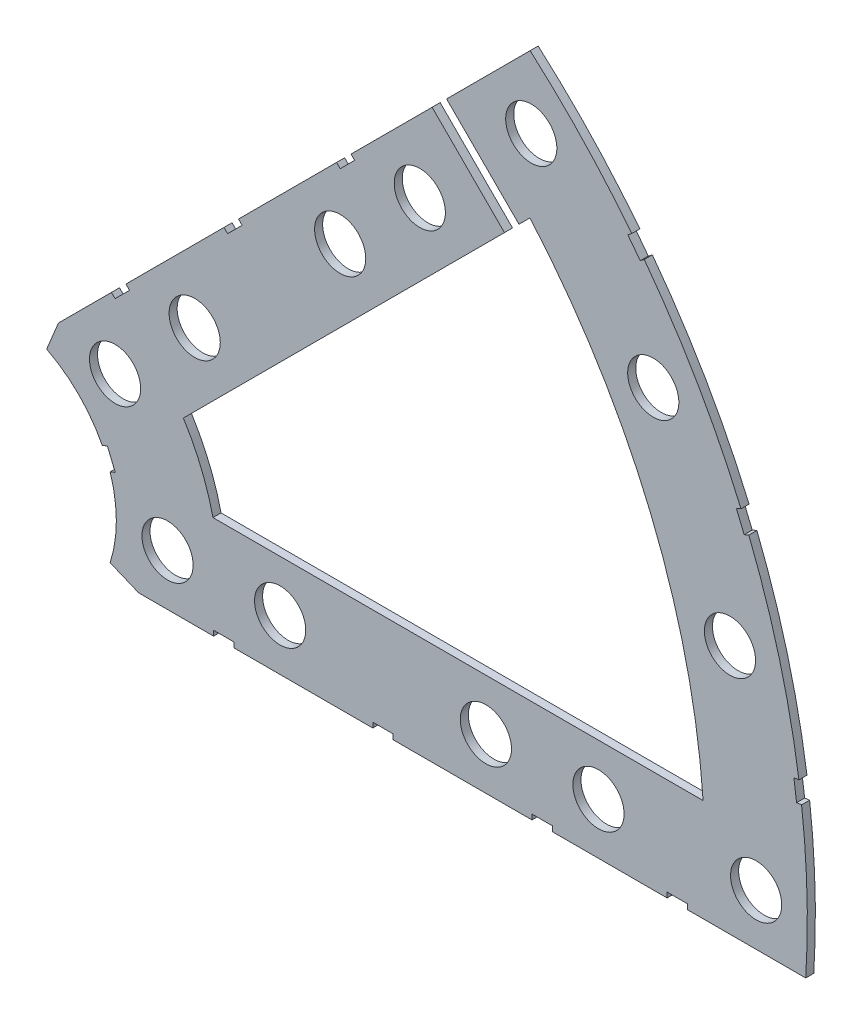
SolidWorks part; units mm, degrees
material "Copper"
ref_plane "Front Plane" through (0, 0, 0) normal (0, 0, 1) x (1, 0, 0)
ref_plane "Top Plane" through (0, 0, 0) normal (0, 1, 0) x (1, 0, 0)
ref_plane "Right Plane" through (0, 0, 0) normal (1, 0, 0) x (0, 0, -1)
sketch "Sketch1" plane through (0, 0, 0) normal (0, 0, 1) x (1, 0, 0)
  line L0 (0, 0) -> (320.3893, 0) construction
  line L1 (0, 0) -> (155.5285, 155.5285) construction
  line L2 (67.2115, 76.1917) -> (8.6967, 17.6769)
  line L3 (8.6967, 17.6769) -> (7.229, 14.1336)
  line L4 (101.4014, -6.35) -> (18.6489, -6.35)
  line L5 (15.1056, -4.8823) -> (18.6489, -6.35)
  line L6 (88.6729, 6.35) -> (27.8605, 6.35)
  line L9 (67.1914, 58.2111) -> (24.1905, 15.2102)
  line L10 (0, 0) -> (40.4486, 97.6516) construction
  line L11 (0, 0) -> (123.4567, -51.1374) construction
  line L18 (8.6967, 17.6769) -> (13.294, 8.6183) construction
  line L19 (18.6489, -6.35) -> (15.4943, 3.3063) construction
  line L20 (27.8605, 6.35) -> (27.7442, 6.7059) construction
  line L21 (24.1905, 15.2102) -> (24.3599, 14.8764) construction
  arc A0 (7.229, 14.1336) -> (15.1056, -4.8823) centre (0, 0) cw
  arc A1 (67.2115, 76.1917) -> (101.4014, -6.35) centre (0, 0) cw
  arc A2 (24.1905, 15.2102) -> (27.8605, 6.35) centre (0, 0) cw
  arc A3 (67.1914, 58.2111) -> (88.6729, 6.35) centre (0, 0) cw
  arc A8 (13.294, 8.6183) -> (15.4943, 3.3063) centre (0, 0) cw construction
  arc A9 (24.3599, 14.8764) -> (27.7442, 6.7059) centre (0, 0) cw construction
  dimension "D1" = 45
  dimension "D3" = 6.35
  dimension "D4" = 15.875
  dimension "D7" = 22.5
  dimension "D8" = 101.6
  dimension "D11" = 12.7
  dimension "D12" = 12.7
  dimension "D2" = 6.35
  dimension "D5" = 67.5
  dimension "D9" = 1.27
  dimension "D10" = 1.27
  dimension "D6" = 12.7
extrude "Boss-Extrude1" add sketch "Sketch1" along normal blind 1
sketch "Sketch2" plane through (0, 0, 1) normal (0, 0, 1) x (1, 0, 0)
  line L0 (0, 0) -> (101.6, 0) construction
  line L1 (0, 0) -> (71.842, 71.842) construction
  line L3 (0, 0) -> (22.225, 0) construction
  line L4 (0, 0) -> (15.7154, 15.7154) construction
  line L5 (0, 0) -> (95.25, 0) construction
  line L6 (0, 0) -> (92.0044, 24.6525) construction
  arc A0 (101.4014, -6.35) -> (67.2115, 76.1917) centre (0, 0) ccw construction
  circle A1 centre (22.225, 0) radius 3.175
  arc A2 (15.1056, -4.8823) -> (7.229, 14.1336) centre (0, 0) ccw construction
  circle A3 centre (36.195, 0) radius 3.175
  circle A4 centre (61.722, 0) radius 3.175
  circle A5 centre (75.692, 0) radius 3.175
  circle A6 centre (95.25, 0) radius 3.175
  circle A7 centre (15.7154, 15.7154) radius 3.175
  circle A8 centre (25.5937, 25.5937) radius 3.175
  circle A9 centre (43.644, 43.644) radius 3.175
  circle A10 centre (53.5223, 53.5223) radius 3.175
  circle A11 centre (92.0044, 24.6525) radius 3.175
  circle A12 centre (82.4889, 47.625) radius 3.175
  circle A13 centre (67.3519, 67.3519) radius 3.175
  dimension "D3" = 6.35
  dimension "D1" = 45
  dimension "D2" = 6.35
  dimension "D4" = 6.35
  dimension "D5" = 13.97
  dimension "D7" = 13.97
  dimension "D8" = 19.558
  dimension "D9" = 45
  dimension "D10" = 15
  dimension "D11" = 25.527
  dimension "D6" = 2
extrude "Cut-Extrude1" cut sketch "Sketch2" against normal through all
sketch "Sketch3" plane through (0, 0, 1) normal (0, 0, 1) x (1, 0, 0)
  line L0 (15.2664, 24.2467) -> (17.0625, 26.0427)
  line L1 (15.2664, 24.2467) -> (15.7154, 23.7977)
  line L2 (17.0625, 26.0427) -> (17.5115, 25.5937)
  line L3 (15.7154, 23.7977) -> (17.5115, 25.5937)
  line L4 (67.2115, 76.1917) -> (8.6967, 17.6769) construction
  line L5 (44.9911, 53.9713) -> (43.195, 52.1753)
  line L6 (44.9911, 53.9713) -> (45.4401, 53.5223)
  line L7 (43.195, 52.1753) -> (43.644, 51.7263)
  line L8 (45.4401, 53.5223) -> (43.644, 51.7263)
  line L9 (27.94, -6.35) -> (30.48, -6.35)
  line L10 (27.94, -6.35) -> (27.94, -5.715)
  line L11 (30.48, -6.35) -> (30.48, -5.715)
  line L12 (27.94, -5.715) -> (30.48, -5.715)
  line L13 (18.6489, -6.35) -> (101.4014, -6.35) construction
  line L14 (67.437, -6.35) -> (69.977, -6.35)
  line L15 (67.437, -6.35) -> (67.437, -5.715)
  line L16 (69.977, -6.35) -> (69.977, -5.715)
  line L17 (67.437, -5.715) -> (69.977, -5.715)
  line L18 (29.2307, 38.211) -> (31.0268, 40.007)
  line L19 (29.2307, 38.211) -> (29.6797, 37.762)
  line L20 (31.0268, 40.007) -> (31.4758, 39.558)
  line L21 (29.6797, 37.762) -> (31.4758, 39.558)
  line L22 (55.049, 64.0292) -> (56.845, 65.8253)
  line L23 (55.049, 64.0292) -> (64.0292, 55.049)
  line L24 (56.845, 65.8253) -> (65.8253, 56.845)
  line L25 (64.0292, 55.049) -> (65.8253, 56.845)
  line L26 (47.6885, -6.35) -> (50.2285, -6.35)
  line L27 (47.6885, -6.35) -> (47.6885, -5.715)
  line L28 (50.2285, -6.35) -> (50.2285, -5.715)
  line L29 (47.6885, -5.715) -> (50.2285, -5.715)
  line L30 (84.201, -6.35) -> (86.741, -6.35)
  line L31 (84.201, -6.35) -> (84.201, -5.715)
  line L32 (86.741, -6.35) -> (86.741, -5.715)
  line L33 (84.201, -5.715) -> (86.741, -5.715)
  line L34 (0, 0) -> (100.7308, 13.2615) construction
  line L35 (0, 0) -> (93.8662, 38.8806) construction
  line L36 (0, 0) -> (80.6047, 61.8502) construction
  line L37 (0, 0) -> (101.6, 0) construction
  line L38 (99.9355, 14.4377) -> (100.267, 11.9194)
  line L39 (99.9355, 14.4377) -> (101.1946, 14.6035)
  line L40 (100.267, 11.9194) -> (101.5261, 12.0852)
  line L41 (101.1946, 14.6035) -> (101.5261, 12.0852)
  line L42 (99.9355, 14.4377) -> (101.5261, 12.0852) construction
  line L43 (100.267, 11.9194) -> (101.1946, 14.6035) construction
  line L44 (93.7655, 37.4643) -> (94.9388, 37.9503)
  line L45 (93.7655, 37.4643) -> (92.7935, 39.811)
  line L46 (94.9388, 37.9503) -> (93.9668, 40.297)
  line L47 (92.7935, 39.811) -> (93.9668, 40.297)
  line L48 (93.7655, 37.4643) -> (93.9668, 40.297) construction
  line L49 (94.9388, 37.9503) -> (92.7935, 39.811) construction
  line L50 (79.3278, 62.4712) -> (80.874, 60.456)
  line L51 (79.3278, 62.4712) -> (80.3354, 63.2443)
  line L52 (80.874, 60.456) -> (81.8816, 61.2292)
  line L53 (80.3354, 63.2443) -> (81.8816, 61.2292)
  line L54 (79.3278, 62.4712) -> (81.8816, 61.2292) construction
  line L55 (80.874, 60.456) -> (80.3354, 63.2443) construction
  line L56 (13.5939, 7.0054) -> (14.5659, 4.6588)
  line L57 (13.5939, 7.0054) -> (14.7672, 7.4914)
  line L58 (14.5659, 4.6588) -> (15.7393, 5.1448)
  line L59 (14.7672, 7.4914) -> (15.7393, 5.1448)
  line L60 (13.5939, 7.0054) -> (15.7393, 5.1448) construction
  line L61 (14.5659, 4.6588) -> (14.7672, 7.4914) construction
  circle A0 centre (15.7154, 15.7154) radius 3.175 construction
  circle A1 centre (43.644, 43.644) radius 3.175 construction
  circle A2 centre (22.225, 0) radius 3.175 construction
  circle A3 centre (61.722, 0) radius 3.175 construction
  arc A4 (101.4014, -6.35) -> (67.2115, 76.1917) centre (0, 0) ccw construction
  circle A7 centre (36.195, 0) radius 3.175 construction
  arc A9 (15.1056, -4.8823) -> (7.229, 14.1336) centre (0, 0) ccw construction
  circle A11 centre (75.692, 0) radius 3.175 construction
  circle A12 centre (25.5937, 25.5937) radius 3.175 construction
  circle A13 centre (53.5223, 53.5223) radius 3.175 construction
  point P75 (14.6666, 6.0751)
  dimension "D2" = 5.715
  dimension "D3" = 2.54
  dimension "D6" = 5.715
  dimension "D8" = 0.635
  dimension "D9" = 5.715
  dimension "D12" = 5.715
  dimension "D4" = 7.5
  dimension "D5" = 22.5
  dimension "D7" = 37.5
  dimension "D10" = 90
  dimension "D11" = 1.27
  dimension "D14" = 0.635
  dimension "D15" = 90
  dimension "D18" = 0.635
  dimension "D19" = 90
  dimension "D22" = 0.635
  dimension "D20" = 1.27
  dimension "D17" = 0.635
  dimension "D13" = 12.7
  dimension "D21" = 2.54
  dimension "D16" = 11.4935
  dimension "D23" = 8.509
  dimension "D24" = 11.4935
  dimension "D25" = 8.509
extrude "Cut-Extrude2" cut sketch "Sketch3" against normal through all
equation "\"cSep\"= 1.005"
equation "\"D11@Sketch2\"=\"cSep\""
equation "\"cSep2\"= \"D8@Sketch2\""
equation "\"D16@Sketch3\"=\"cSep\"/2-.05"
equation "\"D23@Sketch3\"=\"cSep2\"/2-.05"
equation "\"D24@Sketch3\"=\"cSep\"/2-.05"
equation "\"D25@Sketch3\"=\"cSep2\"/2-.05"
